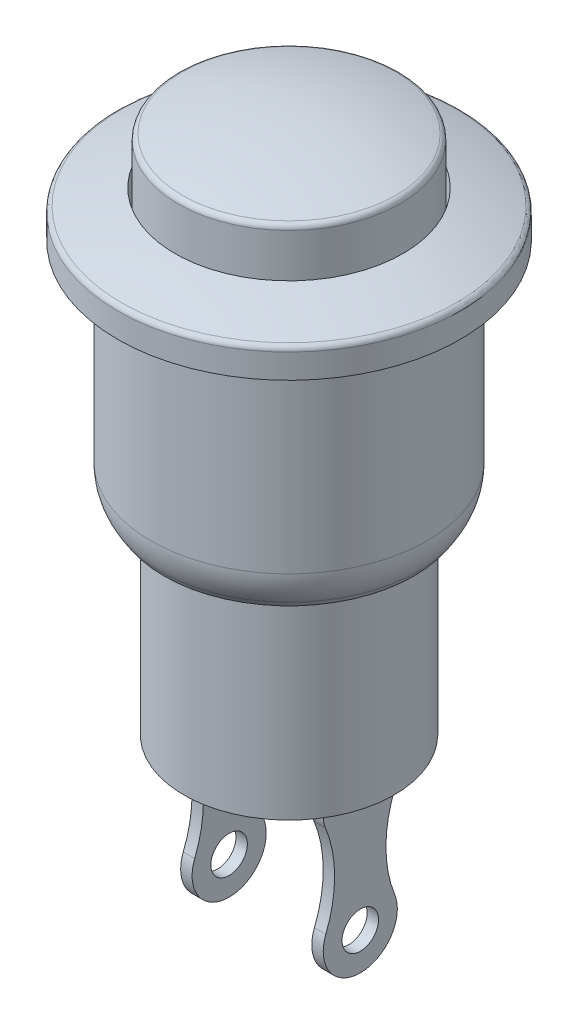
SolidWorks part; units mm, degrees
ref_plane "Plan de face" through (0, 0, 0) normal (0, 0, 1) x (1, 0, 0)
ref_plane "Plan de dessus" through (0, 0, 0) normal (0, 1, 0) x (1, 0, 0)
ref_plane "Plan de droite" through (0, 0, 0) normal (1, 0, 0) x (0, 0, -1)
sketch "Esquisse1" plane through (0, 0, 0) normal (0, 0, 1) x (1, 0, 0)
  line L0 (0, 0) -> (0, 22.281) construction
  line L1 (0, 0) -> (3.69, 0)
  line L2 (3.69, 0) -> (3.69, 7)
  line L3 (3.69, 7) -> (4.84, 7)
  line L4 (4.84, 7) -> (4.84, 15)
  line L5 (4.84, 15) -> (6.01, 15)
  line L6 (6.01, 15) -> (6.01, 16)
  line L7 (4, 16.6) -> (4, 15.0132)
  line L8 (4, 28.4891) -> (4, 11.2832) construction
  line L9 (4, 15.0132) -> (3.89, 15.0132)
  line L10 (3.89, 15.0132) -> (3.89, 18.2)
  line L11 (-3.8266, 18.8) -> (12.3412, 18.8) construction
  line L12 (0, 0) -> (0, -31.1321) construction
  line L13 (0, 18.8) -> (0, 0)
  arc A0 (4, 18.1647) -> (0, 18.8) centre (0, 5.8899) ccw
  arc A1 (6.01, 16) -> (4, 16.6) centre (0, -0.4667) ccw
  point P15 (4, 16.6)
  point P21 (0, 18.8)
  dimension "D1" = 7
  dimension "D2" = 7.38
  dimension "D3" = 9.68
  dimension "D4" = 8
  dimension "D5" = 18.2
  dimension "D6" = 12.02
  dimension "D7" = 1
  dimension "D8" = 4
  dimension "D9" = 18.8
  dimension "D10" = 7.78
  dimension "D11" = 16.6
revolve "Révolution1" add sketch "Esquisse1" angle 360 about L0
fillet "Congé1" radius 0.2 1 edges at (0, 18.2, -3.89)
fillet "Congé2" radius 0.2 1 edges at (0, 16, -6.01)
chamfer "Chanfrein1" distance 0.7 angle 33 1 edges at (0, 7, -4.84)
fillet "Congé3" radius 2 1 edges at (0, 7.7, -4.84)
sketch "Esquisse2" plane through (0, 0, 0) normal (0, -1, 0) x (1, 0, 0)
  line L0 (0, 0) -> (0, 6.3616) construction
  line L1 (2.1, 1.3) -> (2.1, -1.3)
  line L2 (-2.5, 1.3) -> (-2.1, 1.3)
  line L3 (-2.5, 1.3) -> (-2.5, -1.3)
  line L4 (-2.5, -1.3) -> (-2.1, -1.3)
  line L5 (-2.1, 1.3) -> (-2.1, -1.3)
  line L6 (2.5, -1.3) -> (2.1, -1.3)
  line L7 (2.5, 1.3) -> (2.5, -1.3)
  line L8 (2.5, 1.3) -> (2.1, 1.3)
  dimension "D1" = 0.4
  dimension "D2" = 2.6
  dimension "D3" = 1.3
  dimension "D4" = 2.5
extrude "Boss.-Extru.1" add sketch "Esquisse2" along normal blind 6
sketch "Esquisse3" plane through (-2.5, 0, 0) normal (-1, 0, 0) x (0, 0, 1)
  line L0 (-3.5285, -0.8) -> (6.6043, -0.8) construction
  line L1 (-3.69, 0) -> (3.69, 0) construction
  line L2 (-3.2571, -4) -> (6.2876, -4) construction
  line L3 (-1.3, -6) -> (-1.3, 0) construction
  line L4 (1.3, -6) -> (1.3, 0) construction
  line L5 (1.3, -6) -> (-1.3, -6) construction
  line L6 (0, 0) -> (0, -6.5355) construction
  line L7 (1.3, 0) -> (-1.3, 0) construction
  line L8 (-0.9, -1.0754) -> (-0.9, -4.4649) construction
  line L9 (-1.3, -0.8) -> (-4.1925, -0.8)
  line L10 (-4.1925, -0.8) -> (-4.1925, -7.4756)
  line L11 (-4.1925, -7.4756) -> (5.5728, -7.5751)
  line L12 (5.5728, -7.5751) -> (5.2253, -0.8)
  line L13 (5.2253, -0.8) -> (1.3, -0.8)
  arc A0 (-1.2076, -4.2185) -> (1.2076, -4.2185) centre (0, -4.7) ccw
  arc A1 (-1.2076, -4.2185) -> (-1.3, -0.8) centre (-5.2253, -2.6167) ccw
  arc A2 (1.2076, -4.2185) -> (1.3, -0.8) centre (5.2253, -2.6167) cw
  circle A3 centre (0, -4.7) radius 0.64
  point P14 (-1.3, -0.8)
  dimension "D3" = 1.28
  dimension "D1" = 0.8
  dimension "D2" = 4
  dimension ".9" = 0.9
extrude "Enlèv. mat.-Extru.1" cut sketch "Esquisse3" against normal blind 6
fillet "Congé4" radius 1 4 edges at (2.3, -0.8, 1.3) (-2.3, -0.8, 1.3) (2.3, -0.8, -1.3) (-2.3, -0.8, -1.3)
